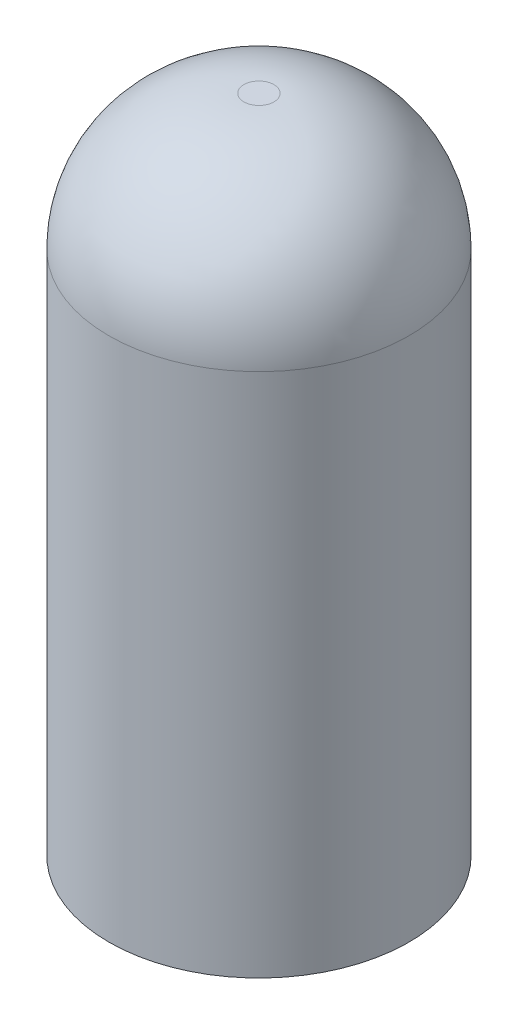
SolidWorks part; units mm, degrees
ref_plane "Front Plane" through (0, 0, 0) normal (0, 0, 1) x (1, 0, 0)
ref_plane "Top Plane" through (0, 0, 0) normal (0, 1, 0) x (1, 0, 0)
ref_plane "Right Plane" through (0, 0, 0) normal (1, 0, 0) x (0, 0, -1)
sketch "Sketch1" plane through (0, 0, 0) normal (0, 1, 0) x (1, 0, 0)
  circle A0 centre (0, 0) radius 6.35
  dimension "D1" = 12.7
extrude "Boss-Extrude1" add sketch "Sketch1" along normal blind 27.94
fillet "Fillet1" radius 5.715 1 edges at (0, 27.94, 6.35)
sketch "Sketch2" plane through (0, 0, 0) normal (0, -1, 0) x (1, 0, 0)
  circle A0 centre (0, 0) radius 1.778
  dimension "D1" = 3.556
extrude "Cut-Extrude1" cut sketch "Sketch2" against normal blind 8.255
